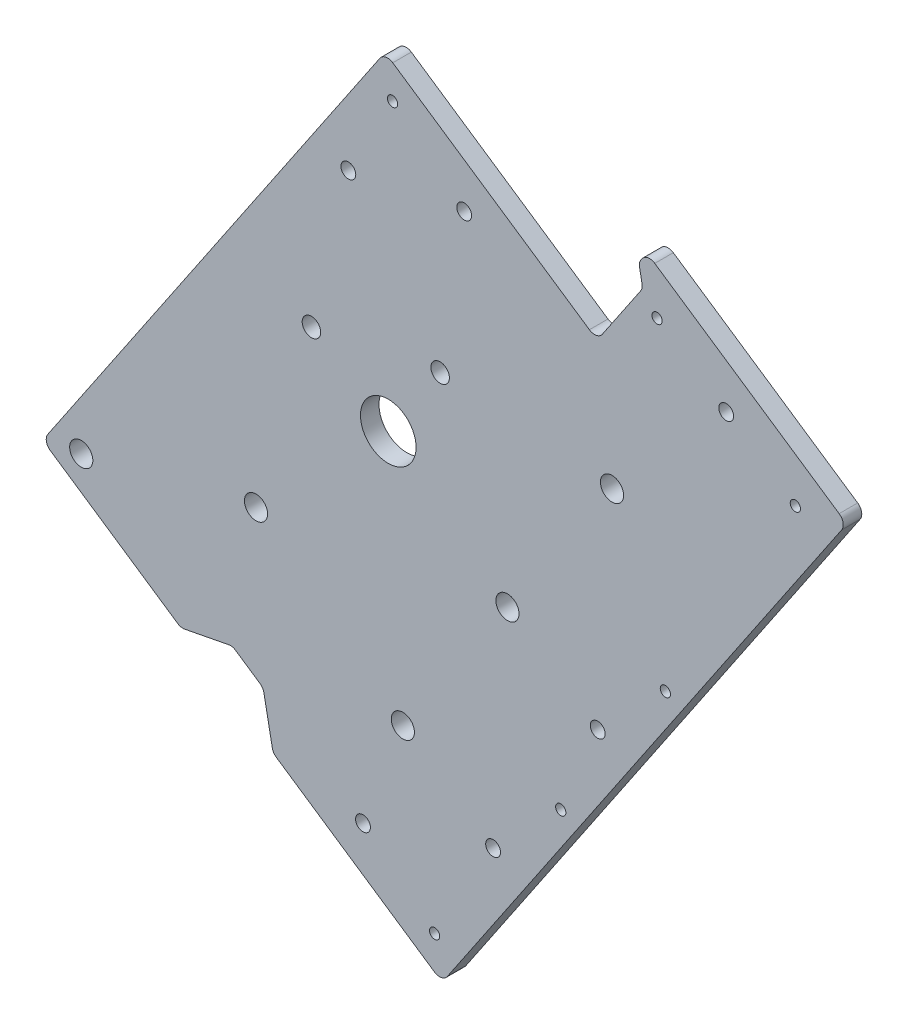
SolidWorks part; units mm, degrees
ref_plane "Front Plane" through (0, 0, 0) normal (0, 0, 1) x (1, 0, 0)
ref_plane "Top Plane" through (0, 0, 0) normal (0, 1, 0) x (1, 0, 0)
ref_plane "Right Plane" through (0, 0, 0) normal (1, 0, 0) x (0, 0, -1)
sketch "Sketch1" plane through (0, 0, 0) normal (0, 0, 1) x (1, 0, 0)
  line L0 (0, 31.75) -> (0, 57.15) construction
  line L1 (31.75, 0) -> (67.31, 0) construction
  line L3 (0, -31.75) -> (0, -97.79) construction
  line L4 (22.4506, -22.4506) -> (58.3717, -58.3717) construction
  line L5 (-22.4506, -22.4506) -> (-72.7401, -72.7401) construction
  line L6 (57.493, 23.8144) -> (29.3332, 12.1502) construction
  line L7 (-40.4112, 40.4112) -> (-22.4506, 22.4506) construction
  line L8 (42.2072, 42.2072) -> (22.4506, 22.4506) construction
  line L9 (71.5729, -29.6465) -> (29.3332, -12.1502) construction
  line L10 (33.5345, -80.9596) -> (12.1502, -29.3332) construction
  line L11 (-37.4226, -90.3462) -> (-12.1502, -29.3332) construction
  circle A0 centre (0, 0) radius 31.75 construction
  circle A3 centre (0, 0) radius 50.8 construction
  dimension "D4" = 63.5
  dimension "D24" = 101.6
  dimension "D2" = 25.4
  dimension "D3" = 35.56
  dimension "D5" = 66.04
  dimension "D6" = 45
  dimension "D7" = 50.8
  dimension "D8" = 71.12
  dimension "D9" = 45
  dimension "D10" = 45
  dimension "D11" = 27.94
  dimension "D12" = 45
  dimension "D13" = 22.5
  dimension "D14" = 22.5
  dimension "D15" = 22.5
  dimension "D16" = 25.4
  dimension "D17" = 45.72
  dimension "D18" = 55.88
  dimension "D19" = 66.04
  dimension "D20" = 22.5
  dimension "D21" = 30.48
sketch "Sketch6" plane through (0, 0, 0) normal (0, 0, 1) x (1, 0, 0)
  line L0 (0, 0) -> (0, 57.15) construction
  line L1 (-68.0069, -76.6709) -> (-109.4868, -48.6565)
  line L2 (-109.4868, -48.6565) -> (-73.9468, 3.9663) construction
  line L3 (-73.9468, 3.9663) -> (-56.6244, -7.7327)
  line L4 (-73.9468, 3.9663) -> (-1.0899, 111.8431)
  line L5 (-1.0899, 111.8431) -> (135.7295, 19.4391)
  line L6 (135.7295, 19.4391) -> (18.4476, -154.2162)
  line L7 (18.4476, -154.2162) -> (-118.3718, -61.8122)
  line L8 (-118.3718, -61.8122) -> (-109.4868, -48.6565)
  arc A0 (0, 57.15) -> (-56.6244, -7.7327) centre (0, 0) ccw
  arc A1 (0, 57.15) -> (70.8293, -29.3385) centre (1.3636, -13.9802) cw
  spline S0 degree 4 poles (72.5802, -14.4204) (72.5732, -14.8939) (72.5509, -15.8408) (72.5026, -17.0238) (72.4142, -18.4418) (72.3202, -19.622) (72.2329, -20.5651) (72.1094, -21.7358) (71.9666, -22.9009) (71.8046, -24.0602) (71.6239, -25.2132) (71.4679, -26.1331) (71.3203, -26.9417) (71.191, -27.6137) (71.0723, -28.2005) (70.9682, -28.6984) (70.8717, -29.1472) (70.8012, -29.4669) (70.7133, -29.8548) (70.619, -30.2629) (70.5011, -30.7621) (70.364, -31.3222) (70.1993, -31.971) (70.0005, -32.7239) (69.7951, -33.4698) (69.582, -34.2143) (69.3614, -34.9567) (69.1333, -35.6968) (68.8388, -36.6189) (68.4706, -37.7207) (68.0195, -38.9988) (67.4748, -40.4488) (66.9013, -41.8877) (66.2993, -43.3149) (65.6691, -44.7298) (65.0111, -46.132) (64.3256, -47.521) (63.613, -48.8963) (62.8736, -50.2574) (62.1078, -51.6038) (61.3159, -52.935) (60.4985, -54.2507) (59.6557, -55.5503) (58.5712, -57.1543) (57.221, -59.0453) (55.576, -61.2004) (53.604, -63.5903) (51.5433, -65.9041) (49.3973, -68.139) (47.1695, -70.2924) (44.8635, -72.3618) (42.4828, -74.3448) (40.0312, -76.2394) (36.8825, -78.4946) (32.9768, -81.016) (28.2508, -83.6809) (21.4155, -86.9191) (14.3083, -89.5267) (6.997, -91.4882) (-0.4519, -92.7974) (-6.6169, -93.4564) (-12.812, -93.702) (-19.0096, -93.5373) (-25.1831, -92.9667) (-31.3064, -91.9964) (-36.5985, -90.8043) (-41.0725, -89.5432) (-44.7523, -88.3359) (-47.6642, -87.2776) (-50.5413, -86.1284) (-53.3811, -84.8896) (-56.1809, -83.563) (-58.5935, -82.3267) (-60.6334, -81.2142) (-62.3138, -80.2525) (-63.6461, -79.4625) (-64.9661, -78.6522) (-66.2736, -77.8217) (-67.4063, -77.0777) (-68.3692, -76.4276) (-69.1659, -75.8779) (-69.7996, -75.4335) (-70.4313, -74.9832) (-71.06, -74.5278) (-71.6725, -74.0775) (-72.2987, -73.6093) (-72.9683, -73.0996) (-73.347, -72.808) (-73.9663, -72.325) (-74.6801, -71.7609) (-75.4046, -71.175) (-76.2838, -70.4507) (-77.1319, -69.735) (-77.9818, -69.0025) (-78.8195, -68.2643) (-79.6511, -67.5155) (-80.4737, -66.7585) (-81.4921, -65.8008) (-82.6974, -64.6343) (-83.8818, -63.4463) (-85.0447, -62.2374) (-85.8084, -61.4205) (-86.1873, -61.0093) (-86.376, -60.8031) knots 0 0 0 0 0 0.008941 0.017882 0.022352 0.026823 0.031293 0.035764 0.044578 0.048985 0.053392 0.057799 0.062207 0.06441 0.066614 0.068817 0.071021 0.072848 0.074676 0.076504 0.078332 0.081987 0.085642 0.089298 0.092953 0.096609 0.100264 0.103919 0.107575 0.114886 0.122197 0.129507 0.136818 0.144129 0.15144 0.158751 0.166062 0.173372 0.180683 0.187994 0.195305 0.202616 0.209927 0.217237 0.231859 0.246481 0.261102 0.275724 0.290346 0.304967 0.319589 0.334211 0.348832 0.363454 0.392697 0.421941 0.451184 0.506141 0.535384 0.564627 0.593871 0.623114 0.652357 0.681601 0.710844 0.740087 0.754709 0.769331 0.783952 0.798574 0.813196 0.827817 0.842439 0.84975 0.857061 0.864371 0.871682 0.878993 0.886304 0.889959 0.893615 0.89727 0.900926 0.904581 0.908237 0.911892 0.915547 0.918186 0.920826 0.926104 0.931382 0.936661 0.941939 0.947217 0.952495 0.957774 0.963052 0.96833 0.978887 0.989443 0.994722 1 1 1 1 1 construction
  spline S1 degree 4 poles (70.8293, -29.3385) (70.8117, -29.4183) (70.776, -29.5781) (70.7133, -29.8548) (70.619, -30.2629) (70.5011, -30.7621) (70.364, -31.3222) (70.1993, -31.971) (70.0005, -32.7239) (69.7951, -33.4698) (69.582, -34.2143) (69.3614, -34.9567) (69.1333, -35.6968) (68.8388, -36.6189) (68.4706, -37.7207) (68.0195, -38.9988) (67.4748, -40.4488) (66.9013, -41.8877) (66.2993, -43.3149) (65.6691, -44.7298) (65.0111, -46.132) (64.3256, -47.521) (63.613, -48.8963) (62.8736, -50.2574) (62.1078, -51.6038) (61.3159, -52.935) (60.4985, -54.2507) (59.6557, -55.5503) (58.5712, -57.1543) (57.221, -59.0453) (55.576, -61.2004) (53.604, -63.5903) (51.5433, -65.9041) (49.3973, -68.139) (47.1695, -70.2924) (44.8635, -72.3618) (42.4828, -74.3448) (40.0312, -76.2394) (36.8825, -78.4946) (32.9768, -81.016) (28.2508, -83.6809) (21.4155, -86.9191) (14.3083, -89.5267) (6.997, -91.4882) (-0.4519, -92.7974) (-6.6169, -93.4564) (-12.812, -93.702) (-19.0096, -93.5373) (-25.1831, -92.9667) (-31.3064, -91.9964) (-36.5985, -90.8043) (-41.0725, -89.5432) (-44.7523, -88.3359) (-47.6642, -87.2776) (-50.5413, -86.1284) (-53.3811, -84.8896) (-56.1809, -83.563) (-58.5935, -82.3267) (-60.6334, -81.2142) (-62.3138, -80.2525) (-63.6461, -79.4625) (-64.9661, -78.6522) (-66.2224, -77.8543) (-67.143, -77.2506) (-67.7363, -76.8537) (-68.0069, -76.6709) knots 0.071021 0.071021 0.071021 0.071021 0.071021 0.072848 0.074676 0.076504 0.078332 0.081987 0.085642 0.089298 0.092953 0.096609 0.100264 0.103919 0.107575 0.114886 0.122197 0.129507 0.136818 0.144129 0.15144 0.158751 0.166062 0.173372 0.180683 0.187994 0.195305 0.202616 0.209927 0.217237 0.231859 0.246481 0.261102 0.275724 0.290346 0.304967 0.319589 0.334211 0.348832 0.363454 0.392697 0.421941 0.451184 0.506141 0.535384 0.564627 0.593871 0.623114 0.652357 0.681601 0.710844 0.740087 0.754709 0.769331 0.783952 0.798574 0.813196 0.827817 0.842439 0.84975 0.857061 0.864371 0.871682 0.878993 0.885158 0.885158 0.885158 0.885158 0.885158
  dimension "D1" = 57.15
  dimension "D2" = 101.6
  dimension "D3" = 63.5
  dimension "D4" = 63.5
  dimension "D5" = 15.875
  dimension "D6" = 101.6
  dimension "D7" = 209.55
extrude "Boss-Extrude2" add sketch "Sketch6" along normal blind 6.35
sketch "Sketch8" plane through (0, 0, 6.35) normal (0, 0, 1) x (1, 0, 0)
  line L0 (-71.0112, -93.7982) -> (-53.3787, -90.3816)
  line L1 (-118.3718, -61.8122) -> (18.4476, -154.2162) construction
  line L2 (-53.3787, -90.3816) -> (-42.8541, -97.4896)
  line L3 (-42.8541, -97.4896) -> (-39.4375, -115.1222)
  line L4 (-39.4375, -115.1222) -> (-71.0112, -93.7982)
  line L5 (18.4476, -154.2162) -> (135.7295, 19.4391) construction
  dimension "D1" = 82.55
  dimension "D2" = 12.7
  dimension "D3" = 12.7
  dimension "D4" = 45
  dimension "D5" = 45
extrude "Cut-Extrude1" cut sketch "Sketch8" against normal through all
sketch "Sketch9" plane through (0, 0, 6.35) normal (0, 0, 1) x (1, 0, 0)
  line L0 (-1.0899, 111.8431) -> (-109.4868, -48.6565)
  line L1 (-1.0899, 111.8431) -> (135.7295, 19.4391)
  line L2 (-109.4868, -48.6565) -> (27.3325, -141.0605)
  line L3 (135.7295, 19.4391) -> (27.3325, -141.0605)
  line L4 (18.4476, -154.2162) -> (135.7295, 19.4391) construction
extrude "Boss-Extrude3" add sketch "Sketch9" against normal through all
sketch "Sketch10" plane through (0, 0, 6.35) normal (0, 0, 1) x (1, 0, 0)
  line L0 (76.6361, 21.2777) -> (4.9965, -84.7966) construction
  line L2 (-39.4375, -115.1222) -> (18.4476, -154.2162) construction
  line L3 (0, 0) -> (-45.2952, -45.2145) construction
  line L4 (-45.2952, -45.2145) -> (4.9965, -84.7966) construction
  line L5 (18.4476, -154.2162) -> (135.7295, 19.4391) construction
  circle A0 centre (4.9965, -84.7966) radius 3.9688
  circle A1 centre (40.8163, -31.7595) radius 3.9687
  circle A2 centre (76.6361, 21.2777) radius 3.9687
  circle A3 centre (-45.2952, -45.2145) radius 3.9687
  dimension "D1" = 7.9375
  dimension "D2" = 50
  dimension "D3" = 50
  dimension "D4" = 128
  dimension "D5" = 64
extrude "Cut-Extrude2" cut sketch "Sketch10" against normal through all
sketch "Sketch11" plane through (0, 0, 6.35) normal (0, 0, 1) x (1, 0, 0)
  circle A0 centre (0, 0) radius 9.525
  dimension "D1" = 19.05
extrude "Cut-Extrude4" cut sketch "Sketch11" against normal through all contours A0
sketch "Sketch12" plane through (0, 0, 6.35) normal (0, 0, 1) x (1, 0, 0)
  line L0 (135.7295, 19.4391) -> (67.3198, 65.6411)
  line L1 (135.7295, 19.4391) -> (157.0534, 51.0128)
  line L2 (67.3198, 65.6411) -> (88.6438, 97.2148)
  line L3 (157.0534, 51.0128) -> (88.6438, 97.2148)
  line L4 (135.7295, 19.4391) -> (-1.0899, 111.8431) construction
  dimension "D1" = 82.55
  dimension "D2" = 38.1
extrude "Boss-Extrude4" add sketch "Sketch12" against normal through all
sketch "Sketch13" plane through (0, 0, 6.35) normal (0, 0, 1) x (1, 0, 0)
  line L0 (40.8163, -31.7595) -> (76.6361, 21.2777) construction
  line L1 (18.4476, -154.2162) -> (157.0534, 51.0128) construction
  line L2 (58.7262, -5.2409) -> (94.8992, -29.6711) construction
  circle A0 centre (94.8992, -29.6711) radius 1.75
  dimension "D1" = 3.5
  dimension "D2" = 6.35
extrude "Cut-Extrude5" cut sketch "Sketch13" against normal through all
pattern_linear "LPattern1" count 2 spacing 64 along (-0.5597, -0.8287, 0) of "Cut-Extrude5"
sketch "Sketch14" plane through (0, 0, 6.35) normal (0, 0, 1) x (1, 0, 0)
  line L0 (59.0794, -82.7083) -> (94.8992, -29.6711) construction
  line L1 (76.9893, -56.1897) -> (71.727, -52.6357) construction
  line L2 (18.4476, -154.2162) -> (157.0534, 51.0128) construction
  line L3 (115.7406, 63.5892) -> (122.8486, 74.1138) construction
  line L4 (157.0534, 51.0128) -> (88.6438, 97.2148) construction
  circle A0 centre (71.727, -52.6357) radius 2.54
  circle A1 centre (35.9072, -105.6729) radius 2.54
  circle A2 centre (115.7406, 63.5892) radius 2.54
  dimension "D1" = 5.08
  dimension "D2" = 12.7
  dimension "D4" = 12.7
  dimension "D3" = 2
extrude "Cut-Extrude6" cut sketch "Sketch14" against normal through all
sketch "Sketch15" plane through (0, 0, 6.35) normal (0, 0, 1) x (1, 0, 0)
  line L0 (-118.3718, -61.8122) -> (-71.0112, -93.7982) construction
  line L1 (-39.4375, -115.1222) -> (18.4476, -154.2162) construction
  line L2 (18.4476, -154.2162) -> (157.0534, 51.0128) construction
  line L3 (-1.0899, 111.8431) -> (-118.3718, -61.8122) construction
  line L4 (67.3198, 65.6411) -> (-1.0899, 111.8431) construction
  circle A0 centre (-105.1473, -59.2498) radius 1.75
  circle A1 centre (15.8851, -140.9917) radius 1.75
  circle A2 centre (59.0794, -82.7083) radius 1.75 construction
  circle A3 centre (1.4726, 98.6186) radius 1.75
  dimension "D1" = 9.525
  dimension "D2" = 9.525
  dimension "D3" = 9.525
  dimension "D4" = 9.525
  dimension "D5" = 9.525
  dimension "D6" = 9.525
extrude "Cut-Extrude7" cut sketch "Sketch15" against normal through all
sketch "Sketch16" plane through (0, 0, 6.35) normal (0, 0, 1) x (1, 0, 0)
  line L0 (157.0534, 51.0128) -> (88.6438, 97.2148) construction
  line L1 (88.6438, 97.2148) -> (67.3198, 65.6411) construction
  line L2 (18.4476, -154.2162) -> (157.0534, 51.0128) construction
  circle A0 centre (92.0604, 79.5822) radius 1.75
  circle A1 centre (139.4209, 47.5962) radius 1.75
  circle A2 centre (94.8992, -29.6711) radius 1.75 construction
  dimension "D1" = 12.7
  dimension "D2" = 12.7
  dimension "D3" = 12.7
  dimension "D4" = 12.7
extrude "Cut-Extrude8" cut sketch "Sketch16" against normal through all
sketch "Sketch17" plane through (0, 0, 6.35) normal (0, 0, 1) x (1, 0, 0)
  line L0 (0, 0) -> (-26.3114, 17.77) construction
  line L1 (0, 0) -> (17.77, 26.3114) construction
  line L2 (18.4476, -154.2162) -> (157.0534, 51.0128) construction
  circle A0 centre (-26.3114, 17.77) radius 1.75
  circle A1 centre (17.77, 26.3114) radius 1.75
  circle A2 centre (94.8992, -29.6711) radius 1.75 construction
  dimension "D1" = 31.75
extrude "Cut-Extrude9" cut sketch "Sketch17" against normal through all
sketch "Sketch19" plane through (0, 0, 6.35) normal (0, 0, 1) x (1, 0, 0)
  line L0 (88.6438, 97.2148) -> (67.3198, 65.6411) construction
  line L1 (67.3198, 65.6411) -> (-1.0899, 111.8431) construction
  line L2 (18.4476, -154.2162) -> (-118.3718, -61.8122) construction
  line L3 (-65.6802, -85.9048) -> (35.6087, 64.0702) construction
  line L4 (-73.9468, 3.9663) -> (-1.0899, 111.8431) construction
  circle A0 centre (35.6087, 64.0702) radius 3.9687 construction
  circle A1 centre (-65.6802, -85.9048) radius 3.9687
  dimension "D1" = 7.9375
  dimension "D2" = 25.4
  dimension "D3" = 19.05
  dimension "D4" = 9.525
extrude "Cut-Extrude11" cut sketch "Sketch19" against normal through all
sketch "Sketch21" plane through (0, 0, 6.35) normal (0, 0, 1) x (1, 0, 0)
  line L0 (-73.9468, 3.9663) -> (-1.0899, 111.8431) construction
  line L1 (67.3198, 65.6411) -> (-1.0899, 111.8431) construction
  line L2 (-118.3718, -61.8122) -> (-71.0112, -93.7982) construction
  line L3 (-39.4375, -115.1222) -> (18.4476, -154.2162) construction
  line L5 (-8.6493, -120.5906) -> (115.7406, 63.5892) construction
  line L6 (18.4476, -154.2162) -> (157.0534, 51.0128) construction
  line L7 (-118.3718, -61.8122) -> (-109.4868, -48.6565) construction
  circle A0 centre (-13.6663, 70.5302) radius 2.54
  circle A1 centre (26.007, 78.2175) radius 2.54
  circle A2 centre (-86.7294, -71.6888) radius 2.54
  circle A3 centre (-8.6493, -120.5906) radius 2.54
  circle A4 centre (35.9072, -105.6729) radius 2.54 construction
  dimension "D1" = 12.7
  dimension "D2" = 12.7
  dimension "D3" = 9.525
  dimension "D4" = 12.7
  dimension "D5" = 41.275
  dimension "D6" = 31.75
  dimension "D7" = 41.275
extrude "Cut-Extrude12" cut sketch "Sketch21" against normal through all
sketch "Sketch22" plane through (0, 0, 6.35) normal (0, 0, 1) x (1, 0, 0)
  circle A0 centre (-26.3114, 17.77) radius 3.175
  circle A1 centre (17.77, 26.3114) radius 3.175
  dimension "D1" = 6.35
extrude "Cut-Extrude13" cut sketch "Sketch22" against normal through all
sketch "Sketch23" plane through (0, 0, 6.35) normal (0, 0, 1) x (1, 0, 0)
  circle A0 centre (-105.1473, -59.2498) radius 3.9688
  dimension "D1" = 7.9375
extrude "Cut-Extrude14" cut sketch "Sketch23" against normal through all
sketch "Sketch24" plane through (0, 0, 6.35) normal (0, 0, 1) x (1, 0, 0)
  circle A0 centre (-86.7294, -71.6888) radius 4.2858
  circle A1 centre (-65.6802, -85.9048) radius 5.6408
extrude "Boss-Extrude5" add sketch "Sketch24" against normal through all
sketch "Sketch25" plane through (0, 0, 6.35) normal (0, 0, 1) x (1, 0, 0)
  line L0 (85.8006, 93.0049) -> (87.1672, 85.9519)
  line L1 (88.6438, 97.2148) -> (67.3198, 65.6411) construction
  line L2 (87.1672, 85.9519) -> (71.5296, 62.7979)
  line L3 (71.5296, 62.7979) -> (67.3198, 65.6411)
  line L4 (67.3198, 65.6411) -> (85.8006, 93.0049)
  line L5 (157.0534, 51.0128) -> (88.6438, 97.2148) construction
  line L6 (67.3198, 65.6411) -> (-1.0899, 111.8431) construction
  dimension "D2" = 45
  dimension "D3" = 5.08
  dimension "D5" = 5.08
extrude "Cut-Extrude15" cut sketch "Sketch25" against normal through all
fillet "Fillet1" radius 3.175 12 edges at (-39.4375, -115.1222, 3.175) (-42.8541, -97.4896, 3.175) (-53.3787, -90.3816, 3.175) (-71.0112, -93.7982, 3.175) (-118.3718, -61.8122, 3.175) (18.4476, -154.2162, 3.175) (-1.0899, 111.8431, 3.175) (157.0534, 51.0128, 3.175) (87.1672, 85.9519, 3.175) (88.6438, 97.2148, 3.175) (85.8006, 93.0049, 3.175) (71.5296, 62.7979, 3.175)
